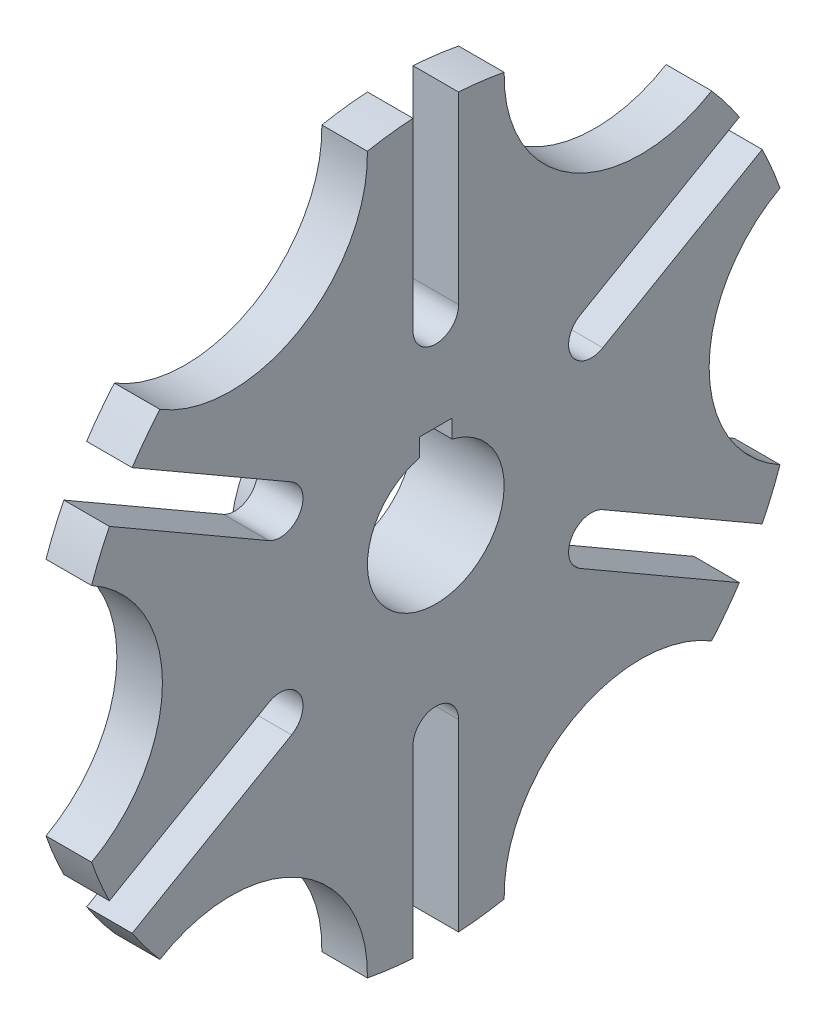
SolidWorks part; units mm, degrees
ref_plane "Front Plane" through (0, 0, 0) normal (0, 0, 1) x (1, 0, 0)
ref_plane "Top Plane" through (0, 0, 0) normal (0, 1, 0) x (1, 0, 0)
ref_plane "Right Plane" through (0, 0, 0) normal (1, 0, 0) x (0, 0, -1)
sketch "Sketch1" plane through (0, 0, 0) normal (0, 0, 1) x (1, 0, 0)
  line L0 (0, 0) -> (0, 31.75)
  line L1 (0, 31.75) -> (6.35, 31.75)
  line L2 (12.7, 38.1) -> (12.7, 101.6)
  line L3 (12.7, 101.6) -> (25.4, 101.6)
  line L4 (25.4, 101.6) -> (25.4, 0)
  line L5 (25.4, 0) -> (0, 0)
  arc A0 (6.35, 31.75) -> (12.7, 38.1) centre (6.35, 38.1) ccw
  point P3 (0, 15.875)
  point P10 (0, 0)
  dimension "D5" = 6.35
  dimension "D1" = 12.7
  dimension "D2" = 101.6
  dimension "D3" = 31.75
  dimension "D4" = 25.4
revolve "Revolve1" add sketch "Sketch1" angle 360 about L5
sketch "Sketch2" plane through (0, 0, 0) normal (-1, 0, 0) x (0, 0, 1)
  circle A0 centre (0, 0) radius 19.05
extrude "Cut-Extrude1" cut sketch "Sketch2" against normal through all
sketch "Sketch3" plane through (12.7, 0, 0) normal (-1, 0, 0) x (0, 0, 1)
  line L0 (-148.4391, 0) -> (150.382, 0) construction
  circle A0 centre (0, 0) radius 114.3
  circle A1 centre (114.3, 0) radius 38.1
  circle A2 centre (57.15, -98.9867) radius 38.1
  circle A3 centre (-57.15, -98.9867) radius 38.1
  circle A4 centre (-114.3, 0) radius 38.1
  circle A5 centre (-57.15, 98.9867) radius 38.1
  circle A6 centre (57.15, 98.9867) radius 38.1
  point P20 (0, 0)
  circle M3 centre (0, 0) radius 101.6
  dimension "D1" = 6
extrude "Cut-Extrude2" cut sketch "Sketch3" against normal through all contours A5 M3 | A6 M3 | A1 L0 M3 | L0 A1 M3 | A2 M3 | A3 M3 | L0 A4 M3 | L0 A4 M3
sketch "Sketch5" plane through (12.7, 0, 0) normal (-1, 0, 0) x (0, 0, 1)
  line L0 (0, 141.2503) -> (0, -132.3129) construction
  line L1 (113.723, 58.3257) -> (46.5477, 19.542)
  line L2 (-6.35, 127.6499) -> (6.35, 127.6499)
  line L3 (-6.35, 127.6499) -> (-6.35, 50.0824)
  line L5 (6.35, 127.6499) -> (6.35, 50.0824)
  line L6 (107.373, 69.3242) -> (40.1977, 30.5405)
  line L7 (107.373, 69.3242) -> (113.723, 58.3257)
  line L8 (107.373, -69.3242) -> (40.1977, -30.5405)
  line L9 (113.723, -58.3257) -> (46.5477, -19.542)
  line L10 (113.723, -58.3257) -> (107.373, -69.3242)
  line L11 (-6.35, -127.6499) -> (-6.35, -50.0824)
  line L12 (6.35, -127.6499) -> (6.35, -50.0824)
  line L13 (6.35, -127.6499) -> (-6.35, -127.6499)
  line L14 (-113.723, -58.3257) -> (-46.5477, -19.542)
  line L15 (-107.373, -69.3242) -> (-40.1977, -30.5405)
  line L16 (-107.373, -69.3242) -> (-113.723, -58.3257)
  line L17 (-107.373, 69.3242) -> (-40.1977, 30.5405)
  line L18 (-113.723, 58.3257) -> (-46.5477, 19.542)
  line L19 (-113.723, 58.3257) -> (-107.373, 69.3242)
  arc A1 (-6.35, 50.0824) -> (6.35, 50.0824) centre (0, 50.0824) ccw
  arc A2 (40.1977, 30.5405) -> (46.5477, 19.542) centre (43.3727, 25.0412) ccw
  arc A3 (46.5477, -19.542) -> (40.1977, -30.5405) centre (43.3727, -25.0412) ccw
  arc A4 (6.35, -50.0824) -> (-6.35, -50.0824) centre (0, -50.0824) ccw
  arc A5 (-40.1977, -30.5405) -> (-46.5477, -19.542) centre (-43.3727, -25.0412) ccw
  arc A6 (-46.5477, 19.542) -> (-40.1977, 30.5405) centre (-43.3727, 25.0412) ccw
  point P9 (0, 127.6499)
  point P37 (0, 0)
  dimension "D1" = 6
extrude "Cut-Extrude5" cut sketch "Sketch5" against normal through all
sketch "Sketch6" plane through (0, 0, 0) normal (-1, 0, 0) x (0, 0, 1)
  line L1 (-4.572, 18.4932) -> (4.572, 18.4932)
  line L2 (-4.572, 18.4932) -> (-4.572, 23.5732)
  line L3 (-4.572, 23.5732) -> (4.572, 23.5732)
  line L4 (4.572, 18.4932) -> (4.572, 23.5732)
  circle A4 centre (0, 0) radius 19.05 construction
  point P4 (0, 18.4932)
  point P5 (0, 0)
  dimension "D1" = 9.144
  dimension "D2" = 5.08
extrude "Cut-Extrude6" cut sketch "Sketch6" against normal through all
